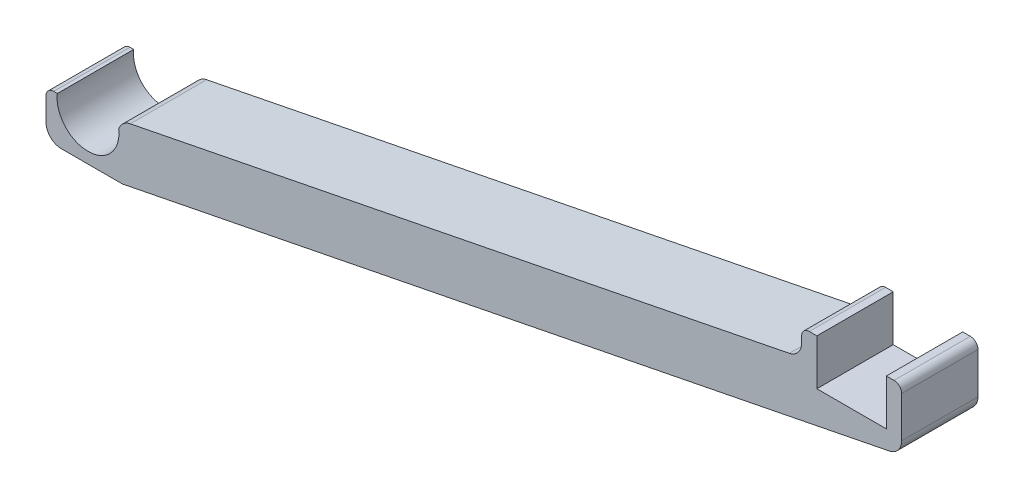
SolidWorks part; units mm, degrees
ref_plane "Спереди" through (0, 0, 0) normal (0, 0, 1) x (1, 0, 0)
ref_plane "Сверху" through (0, 0, 0) normal (0, 1, 0) x (1, 0, 0)
ref_plane "Справа" through (0, 0, 0) normal (1, 0, 0) x (0, 0, -1)
sketch "Эскиз1" plane through (0, 0, 0) normal (0, 0, 1) x (1, 0, 0)
  line L9 (95.45, 22.75) -> (95.45, 16.75)
  line L11 (93.45, 19.287) -> (93.45, 22.75)
  line L12 (93.45, 22.75) -> (95.45, 22.75)
  line L13 (106.55, 14.75) -> (106.55, 22.75)
  line L14 (95.45, 16.75) -> (104.55, 16.75)
  line L15 (104.55, 16.75) -> (104.55, 22.75)
  line L16 (104.55, 22.75) -> (106.55, 22.75)
  line L17 (4.5, -5.5) -> (106.55, 14.75)
  line L19 (-5.5, 0.5) -> (-5.5, -5.5)
  line L20 (-5.5, -5.5) -> (4.5, -5.5)
  line L22 (4.4935, 1.6352) -> (93.45, 19.287)
  line L23 (-4.019, 0.5) -> (-5.5, 0.5)
  line L24 (4.019, 0.5) -> (4.4935, 1.6352)
  arc A0 (-4.019, 0.5) -> (4.019, 0.5) centre (0, 0) ccw
  point P10 (100, 16.75)
  dimension "D7" = 8.1
  dimension "D9" = 5.5
  dimension "D2" = 9.1
  dimension "D3" = 16.75
  dimension "D4" = 0.5
  dimension "D5" = 2
  dimension "D6" = 6
  dimension "D8" = 5.5
  dimension "D10" = 100
  dimension "D11" = 7
  dimension "D12" = 10
  dimension "D13" = 8
extrude "Бобышка-Вытянуть1" add sketch "Эскиз1" along normal blind 10
fillet "Скругление1" radius 2 5 edges at (106.55, 14.75, 5) (4.5, -5.5, 5) (-5.5, -5.5, 5) (4.4935, 1.6352, 5) (93.45, 19.287, 5)
fillet "Скругление2" radius 1 3 edges at (-5.5, 0.5, 5) (93.45, 22.75, 5) (106.55, 22.75, 5)
